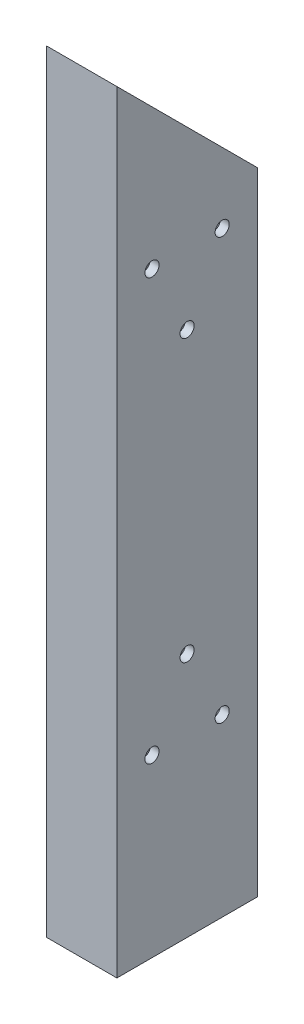
SolidWorks part; units mm, degrees
ref_plane "Front Plane" through (0, 0, 0) normal (0, 0, 1) x (1, 0, 0)
ref_plane "Top Plane" through (0, 0, 0) normal (0, 1, 0) x (1, 0, 0)
ref_plane "Right Plane" through (0, 0, 0) normal (1, 0, 0) x (0, 0, -1)
sketch "Sketch1" plane through (0, 0, 0) normal (0, 1, 0) x (1, 0, 0)
  line L1 (0, 0) -> (25.4, 0)
  line L2 (0, 0) -> (0, 50.8)
  line L3 (0, 50.8) -> (25.4, 50.8)
  line L4 (25.4, 0) -> (25.4, 50.8)
  line L5 (3.175, 3.175) -> (22.225, 3.175)
  line L6 (3.175, 3.175) -> (3.175, 47.625)
  line L7 (3.175, 47.625) -> (22.225, 47.625)
  line L8 (22.225, 3.175) -> (22.225, 47.625)
  dimension "D1" = 25.4
  dimension "D2" = 50.8
  dimension "D3" = 3.175
  dimension "D4" = 3.175
  dimension "D5" = 3.175
  dimension "D6" = 3.175
extrude "Boss-Extrude1" add sketch "Sketch1" along normal blind 279.4
sketch "Sketch2" plane through (25.4, 0, 0) normal (1, 0, 0) x (0, 0, -1)
  line L0 (0, 279.4) -> (50.8, 228.6)
  line L1 (50.8, 279.4) -> (50.8, 0) construction
  line L3 (0, 279.4) -> (50.8, 279.4)
  line L4 (50.8, 279.4) -> (50.8, 228.6)
  dimension "D1" = 228.6
extrude "Cut-Extrude1" cut sketch "Sketch2" against normal blind 279.4
sketch "Sketch3" plane through (25.4, 0, 0) normal (1, 0, 0) x (0, 0, -1)
  line L0 (50.8, 228.6) -> (0, 228.6) construction
  line L1 (0, 279.4) -> (0, 0) construction
  line L2 (12.7, 215.9) -> (38.1, 215.9) construction
  line L3 (25.4, 215.9) -> (25.4, 190.5) construction
  line L4 (0, 50.8) -> (50.8, 50.8) construction
  line L5 (50.8, 228.6) -> (50.8, 0) construction
  line L6 (0, 0) -> (50.8, 0) construction
  line L7 (12.7, 63.5) -> (38.1, 63.5) construction
  line L8 (25.4, 88.9) -> (25.4, 63.5) construction
  circle A0 centre (12.7, 215.9) radius 2.5527
  circle A1 centre (38.1, 215.9) radius 2.5527
  circle A2 centre (25.4, 190.5) radius 2.5527
  circle A3 centre (12.7, 63.5) radius 2.5527
  circle A4 centre (38.1, 63.5) radius 2.5527
  circle A5 centre (25.4, 88.9) radius 2.5527
  point P12 (25.4, 228.6)
  point P25 (25.4, 50.8)
  dimension "D1" = 5.1054
  dimension "D2" = 25.4
  dimension "D3" = 25.4
  dimension "D4" = 12.7
  dimension "D5" = 50.8
  dimension "D6" = 25.4
  dimension "D7" = 25.4
  dimension "D8" = 12.7
extrude "Cut-Extrude2" cut sketch "Sketch3" against normal blind 25.4
